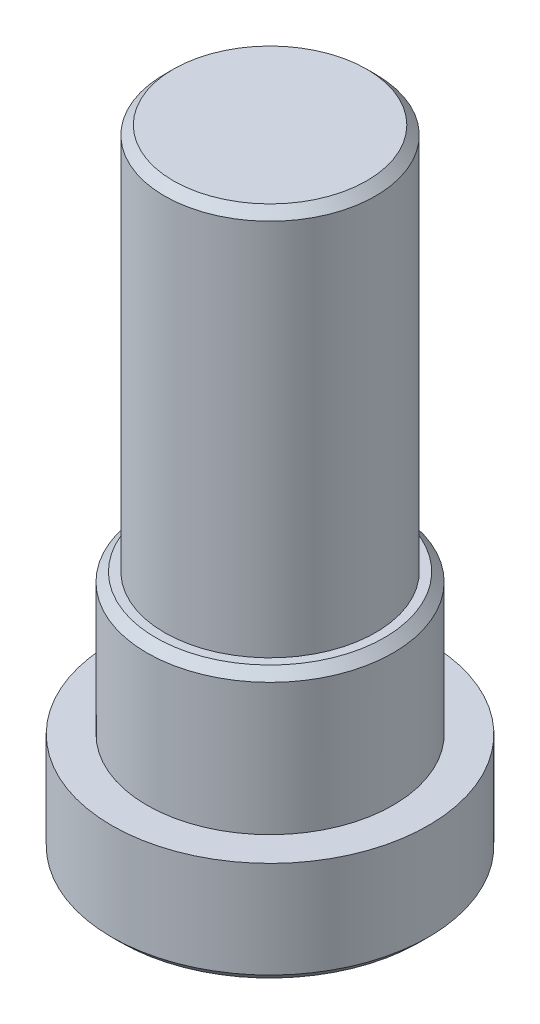
SolidWorks part; units mm, degrees
material "Plain Carbon Steel"
ref_plane "Front" through (0, 0, 0) normal (0, 0, 1) x (1, 0, 0)
ref_plane "Top" through (0, 0, 0) normal (0, 1, 0) x (1, 0, 0)
ref_plane "Right" through (0, 0, 0) normal (1, 0, 0) x (0, 0, -1)
sketch "Sketch1" plane through (0, 0, 0) normal (0, 0, 1) x (1, 0, 0)
  line L0 (0, 0) -> (0, 9)
  line L1 (0, 9) -> (1.5, 9)
  line L2 (1.5, 9) -> (1.5, 3.5)
  line L3 (1.5, 3.5) -> (1.75, 3.5)
  line L4 (1.75, 3.5) -> (1.75, 1.5)
  line L5 (1.75, 1.5) -> (2.25, 1.5)
  line L6 (2.25, 1.5) -> (2.25, 0)
  line L7 (2.25, 0) -> (0, 0)
  line L8 (0, 0) -> (0, -19.6914) construction
  dimension "D1" = 9
  dimension "D2" = 1.5
  dimension "D3" = 2
  dimension "D4" = 3
  dimension "D5" = 3.5
  dimension "D6" = 4.5
revolve "Revolve1" add sketch "Sketch1" angle 360 about L8
sketch "Sketch2" plane through (0, 0, 0) normal (0, -1, 0) x (1, 0, 0)
  line L1 (1.1547, 0) -> (0.5774, 1)
  line L2 (0.5774, 1) -> (-0.5774, 1)
  line L3 (-0.5774, 1) -> (-1.1547, 0)
  line L4 (-1.1547, 0) -> (-0.5774, -1)
  line L5 (-0.5774, -1) -> (0.5774, -1)
  line L6 (0.5774, -1) -> (1.1547, 0)
  circle A0 centre (0, 0) radius 1 construction
  dimension "D1" = 2
extrude "Cut-Extrude1" cut sketch "Sketch2" against normal blind 1
chamfer "Chamfer1" distance 0.125 3 edges at (0, 9, 1.5) (0, 3.5, 1.75) (0, 0, 2.25)
